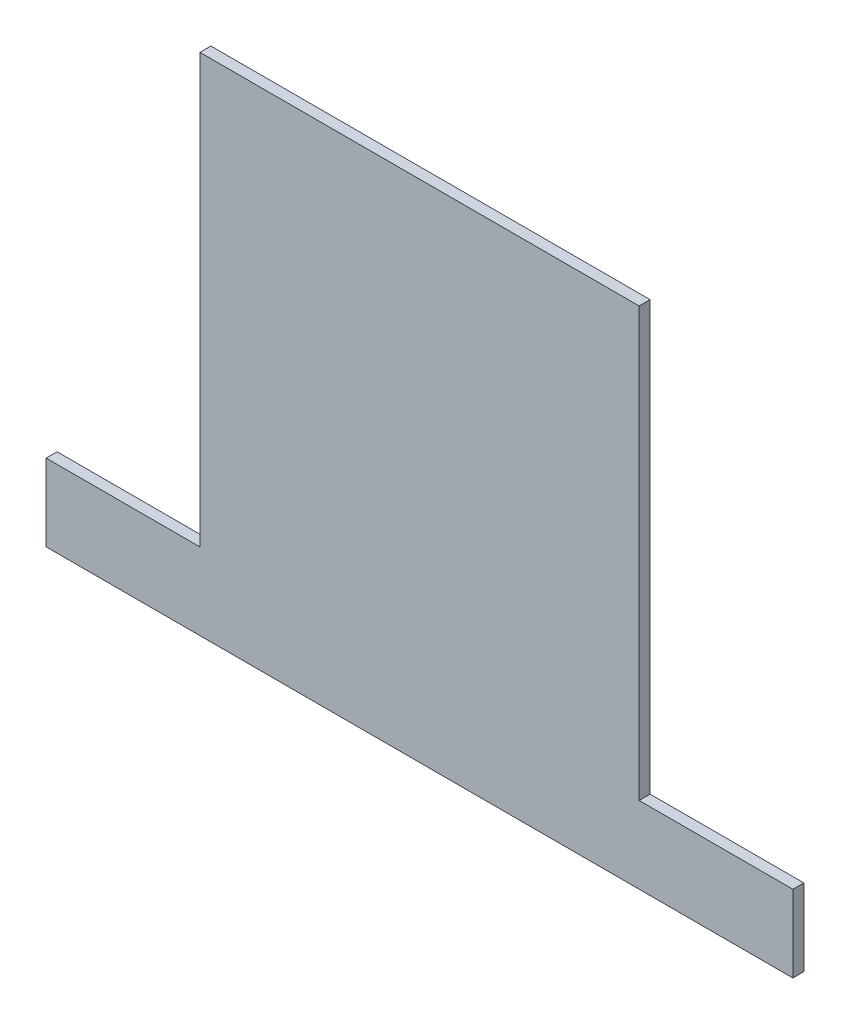
SolidWorks part; units mm, degrees
ref_plane "Front Plane" through (0, 0, 0) normal (0, 0, 1) x (1, 0, 0)
ref_plane "Top Plane" through (0, 0, 0) normal (0, 1, 0) x (1, 0, 0)
ref_plane "Right Plane" through (0, 0, 0) normal (1, 0, 0) x (0, 0, -1)
sketch "Sketch1" plane through (0, 0, 0) normal (0, 0, 1) x (1, 0, 0)
  line L1 (0, 0) -> (431.8, 0)
  line L2 (0, 0) -> (0, 292.1)
  line L3 (0, 292.1) -> (431.8, 292.1)
  line L4 (431.8, 0) -> (431.8, 292.1)
  dimension "D1" = 292.1
  dimension "D2" = 431.8
extrude "Boss-Extrude1" add sketch "Sketch1" along normal blind 6.35
sketch "Sketch2" plane through (0, 0, 6.35) normal (0, 0, 1) x (1, 0, 0)
  line L0 (431.8, 0) -> (431.8, 292.1) construction
  line L1 (0, 292.1) -> (88.9, 292.1)
  line L2 (0, 292.1) -> (0, 44.45)
  line L3 (0, 44.45) -> (88.9, 44.45)
  line L4 (88.9, 292.1) -> (88.9, 44.45)
  line L5 (431.8, 44.45) -> (342.9, 44.45)
  line L6 (431.8, 44.45) -> (431.8, 292.1)
  line L7 (431.8, 292.1) -> (342.9, 292.1)
  line L8 (342.9, 44.45) -> (342.9, 292.1)
  line L9 (431.8, 292.1) -> (0, 292.1) construction
  line L10 (0, 0) -> (431.8, 0) construction
  dimension "D1" = 254
  dimension "D2" = 44.45
extrude "Cut-Extrude1" cut sketch "Sketch2" against normal through all
